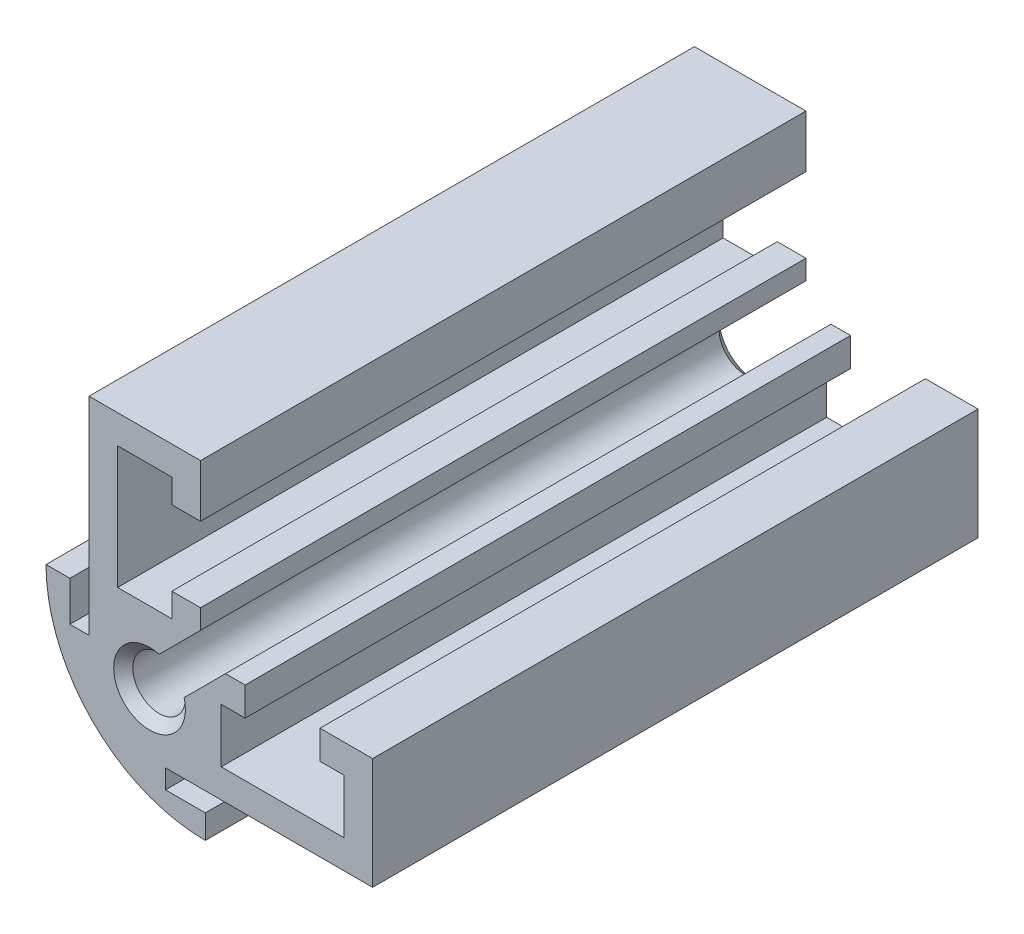
SolidWorks part; units mm, degrees
material "7079 Alloy"
ref_plane "Front" through (0, 0, 0) normal (0, 0, 1) x (1, 0, 0)
ref_plane "Top" through (0, 0, 0) normal (0, 1, 0) x (1, 0, 0)
ref_plane "Right" through (0, 0, 0) normal (1, 0, 0) x (0, 0, -1)
sketch "Sketch1" plane through (0, 0, 0) normal (0, 0, 1) x (1, 0, 0)
  line L0 (10.25, -10.25) -> (-10.25, 10.25) construction
  line L1 (-10.25, 10.25) -> (10.25, 10.25)
  line L2 (-10.25, 10.25) -> (-10.25, -0.25)
  line L3 (-0.25, -10.25) -> (10.25, -10.25)
  line L4 (10.25, 10.25) -> (10.25, -10.25)
  arc A0 (-10.25, -0.25) -> (-0.25, -10.25) centre (-0.25, -0.25) ccw
  point P7 (-10.25, -10.25)
  dimension "D3" = 10
  dimension "D1" = 20.5
  dimension "D2" = 20.5
extrude "Extrude1" add sketch "Sketch1" along normal mid plane 38
sketch "Sketch2" plane through (0, 0, 19) normal (0, 0, 1) x (1, 0, 0)
  line L0 (10.25, -7.55) -> (-2.75, -7.55)
  line L1 (10.25, -10.25) -> (10.25, 10.25) construction
  line L2 (-2.75, -7.55) -> (-2.75, -8.75)
  line L3 (-2.75, -8.75) -> (-0.25, -8.75)
  line L4 (-0.25, -8.75) -> (-0.25, -10.25)
  line L5 (-0.25, -10.25) -> (10.25, -10.25) construction
  line L6 (-7.55, 10.25) -> (-7.55, -2.75)
  line L7 (10.25, 10.25) -> (-10.25, 10.25) construction
  line L8 (-7.55, -2.75) -> (-8.75, -2.75)
  line L9 (-8.75, -2.75) -> (-8.75, -0.25)
  line L10 (-8.75, -0.25) -> (-10.25, -0.25)
  line L11 (-10.25, 10.25) -> (-10.25, -0.25) construction
  line L12 (-7.55, 10.25) -> (-10.25, 10.25)
  line L13 (-10.25, 10.25) -> (-10.25, -0.25)
  line L14 (-0.25, -10.25) -> (10.25, -10.25)
  line L15 (10.25, -10.25) -> (10.25, -7.55)
  dimension "D1" = 13
  dimension "D2" = 1.5
  dimension "D3" = 2.5
  dimension "D4" = 1.2
  dimension "D5" = 13
  dimension "D6" = 1.5
  dimension "D7" = 1.2
  dimension "D8" = 2.5
extrude "Cut-Extrude1" cut sketch "Sketch2" against normal through all
sketch "Sketch3" plane through (0, 0, 19) normal (0, 0, 1) x (1, 0, 0)
  line L0 (-0.55, 10.25) -> (-0.55, 6.95)
  line L1 (10.25, -7.55) -> (10.25, 10.25) construction
  line L2 (10.25, -0.55) -> (6.95, -0.55)
  line L3 (6.95, -0.55) -> (6.95, -2.35)
  line L4 (6.95, -2.35) -> (8.45, -2.35)
  line L5 (8.45, -2.35) -> (8.45, -5.75)
  line L6 (8.45, -5.75) -> (0.75, -5.75)
  line L7 (0.75, -5.75) -> (0.75, -2.35)
  line L8 (0.75, -2.35) -> (2.25, -2.35)
  line L9 (2.25, -2.35) -> (2.25, -0.55)
  line L10 (2.25, -0.55) -> (1.02, -0.55)
  line L11 (1.02, -0.55) -> (-2.2517, -3.8217)
  line L12 (10.25, 10.25) -> (-7.55, 10.25) construction
  line L13 (-0.55, 6.95) -> (-2.35, 6.95)
  line L14 (-2.35, 6.95) -> (-2.35, 8.45)
  line L15 (-2.35, 8.45) -> (-5.75, 8.45)
  line L16 (-5.75, 8.45) -> (-5.75, 0.75)
  line L17 (-5.75, 0.75) -> (-2.35, 0.75)
  line L18 (-2.35, 0.75) -> (-2.35, 2.25)
  line L19 (-2.35, 2.25) -> (-0.55, 2.25)
  line L20 (-0.55, 2.25) -> (-0.55, 1.02)
  line L21 (-0.55, 1.02) -> (-3.8217, -2.2517)
  line L22 (-7.55, -2.75) -> (-7.55, 10.25) construction
  line L23 (10.25, -0.55) -> (10.25, 10.25)
  line L24 (10.25, 10.25) -> (-0.55, 10.25)
  arc A0 (-3.8217, -2.2517) -> (-2.2517, -3.8217) centre (-3.75, -3.75) ccw
  dimension "D11" = 3
  dimension "D12" = 6.5
  dimension "D13" = 6.5
  dimension "D2" = 3.3
  dimension "D3" = 1.8
  dimension "D4" = 7.7
  dimension "D5" = 3.4
  dimension "D6" = 3.4
  dimension "D7" = 1.5
  dimension "D8" = 1.8
  dimension "D9" = 1.5
  dimension "D10" = 1.23
  dimension "D14" = 7
  dimension "D15" = 7
  dimension "D16" = 3.3
  dimension "D17" = 1.8
  dimension "D18" = 1.5
  dimension "D19" = 3.4
  dimension "D20" = 7.7
  dimension "D21" = 3.4
  dimension "D22" = 1.5
  dimension "D23" = 1.8
  dimension "D24" = 1.23
  dimension "D25" = 45
  dimension "D26" = 45
extrude "Cut-Extrude2" cut sketch "Sketch3" against normal through all
hole_wizard "Furo roscado de M41" positions "Esboço2" profile "Esboço1" tap size "M4" standard "ISO" end condition through all
sketch "Esboço2" plane through (0, 0, 19) normal (0, 0, 1) x (1, 0, 0)
  arc A0 (-3.8217, -2.2517) -> (-2.2517, -3.8217) centre (-3.75, -3.75) ccw construction
  point P0 (-3.75, -3.75)
sketch "Esboço1" plane through (-3.75, -3.75, 19) normal (1, 0, 0) x (0, -1, 0)
  line L0 (0, 0) -> (0, 38)
  line L1 (0, 38) -> (2.25, 38)
  line L2 (1.65, 37.4) -> (1.65, 0.6)
  line L3 (1.65, 0.6) -> (2.25, 0)
  line L5 (2.25, 0) -> (0, 0)
  line L6 (-1.65, 0.6) -> (-2.25, 0) construction
  line L7 (2.25, 38) -> (1.65, 37.4)
  line L8 (-2.25, 38) -> (-1.65, 37.4) construction
  line L11 (0, -6.35) -> (0, 107.95) construction
  dimension "Thru Tap Drill Dia." = 3.3
  dimension "Thru Tap Drill Depth" = 38
  dimension "Near C'Sink Dia." = 4.5
  dimension "Near C'Sink Angle" = 90
  dimension "Far C'Sink Dia." = 4.5
  dimension "Far C'Sink Angle" = 90
cosmetic thread "Rosca de furo1" parameters "D2"=4
